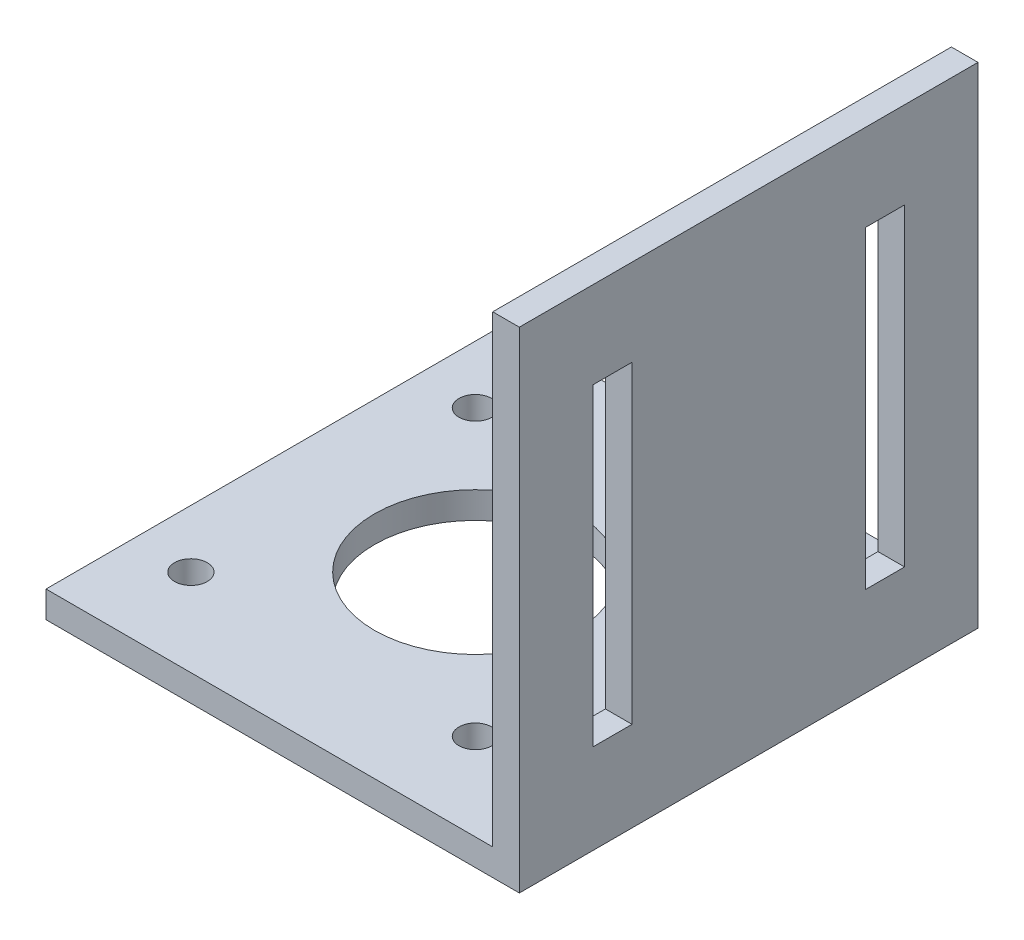
SolidWorks part; units mm, degrees
ref_plane "Front Plane" through (0, 0, 0) normal (0, 0, 1) x (1, 0, 0)
ref_plane "Top Plane" through (0, 0, 0) normal (0, 1, 0) x (1, 0, 0)
ref_plane "Right Plane" through (0, 0, 0) normal (1, 0, 0) x (0, 0, -1)
sketch "Sketch1" plane through (0, 0, 0) normal (0, 1, 0) x (1, 0, 0)
  line L1 (0, 0) -> (51.58, 0)
  line L2 (0, 0) -> (0, 49.98)
  line L3 (0, 49.98) -> (51.58, 49.98)
  line L4 (51.58, 0) -> (51.58, 49.98)
  line L5 (0, 0) -> (51.58, 49.98) construction
  line L6 (0, 49.98) -> (51.58, 0) construction
  point P4 (25.79, 24.99)
  dimension "D1" = 49.98
  dimension "D2" = 51.58
extrude "Boss-Extrude1" add sketch "Sketch1" along normal blind 2.9
sketch "Sketch2" plane through (0, 2.9, 0) normal (0, 1, 0) x (1, 0, 0)
  line L0 (51.58, 49.98) -> (0, 49.98) construction
  line L1 (51.58, 0) -> (48.68, 0)
  line L2 (51.58, 0) -> (51.58, 49.98)
  line L3 (51.58, 49.98) -> (48.68, 49.98)
  line L4 (48.68, 0) -> (48.68, 49.98)
  line L5 (51.58, 0) -> (48.68, 49.98) construction
  line L6 (51.58, 49.98) -> (48.68, 0) construction
  point P4 (50.13, 24.99)
  dimension "D1" = 2.9
extrude "Boss-Extrude2" add sketch "Sketch2" along normal blind 50.5
ref_plane "Plane1" through (51.58, 53.4, -49.98) normal (0, 0, -1) x (-1, 0, 0)
sketch "Sketch4" plane through (51.58, 0, 0) normal (1, 0, 0) x (0, 0, -1)
  line L0 (0, 53.4) -> (0, 0) construction
  line L1 (8, 43.95) -> (12.28, 43.95)
  line L2 (8, 43.95) -> (8, 9.78)
  line L3 (8, 9.78) -> (12.28, 9.78)
  line L4 (12.28, 43.95) -> (12.28, 9.78)
  line L5 (49.98, 53.4) -> (49.98, 0) construction
  line L6 (0, 53.4) -> (49.98, 53.4) construction
  line L7 (37.7, 43.95) -> (41.98, 43.95)
  line L8 (37.7, 43.95) -> (37.7, 9.78)
  line L9 (37.7, 9.78) -> (41.98, 9.78)
  line L10 (41.98, 43.95) -> (41.98, 9.78)
  dimension "D1" = 8
  dimension "D2" = 8
  dimension "D3" = 4.28
  dimension "D4" = 9.45
  dimension "D5" = 34.17
  dimension "D6" = 9.45
extrude "Cut-Extrude1" cut sketch "Sketch4" against normal through all
sketch "Sketch5" plane through (0, 0, 0) normal (0, -1, 0) x (1, 0, 0)
  line L0 (0, -24.99) -> (51.58, -24.99) construction
  line L1 (0, -49.98) -> (0, 0) construction
  line L2 (51.58, 0) -> (51.58, -49.98) construction
  line L3 (21.8, -49.98) -> (21.8, 0) construction
  line L4 (51.58, -49.98) -> (0, -49.98) construction
  line L5 (0, 0) -> (51.58, 0) construction
  circle A0 centre (21.8, -24.99) radius 11
  circle A1 centre (6.3, -40.49) radius 1.785
  circle A2 centre (37.3, -40.49) radius 1.785
  circle A3 centre (37.3, -9.49) radius 1.785
  circle A4 centre (6.3, -9.49) radius 1.785
  dimension "D1" = 21.8
  dimension "D2" = 22
  dimension "D3" = 3.57
  dimension "D4" = 31
  dimension "D5" = 31
extrude "Cut-Extrude2" cut sketch "Sketch5" against normal through all
